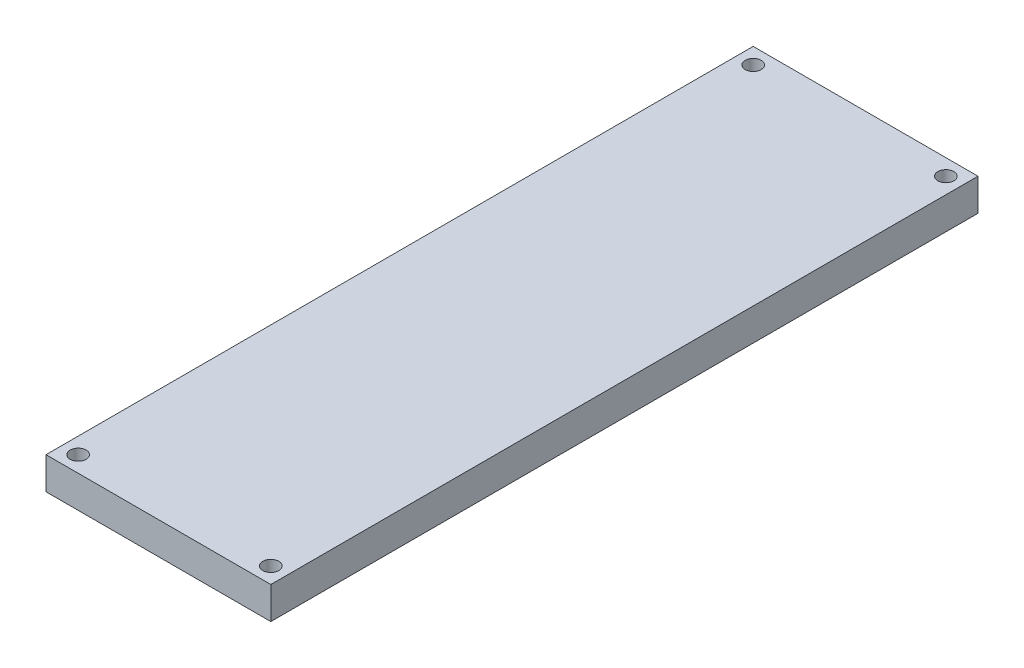
SolidWorks part; units mm, degrees
material "6061-T6 (SS)"
ref_plane "Front Plane" through (0, 0, 0) normal (0, 0, 1) x (1, 0, 0)
ref_plane "Top Plane" through (0, 0, 0) normal (0, 1, 0) x (1, 0, 0)
ref_plane "Right Plane" through (0, 0, 0) normal (1, 0, 0) x (0, 0, -1)
sketch "Sketch1" plane through (0, 0, 0) normal (0, 1, 0) x (1, 0, 0)
  line L1 (44.4136, -139.7) -> (-44.4136, -139.7)
  line L2 (44.4136, -139.7) -> (44.4136, 139.7)
  line L3 (44.4136, 139.7) -> (-44.4136, 139.7)
  line L4 (-44.4136, -139.7) -> (-44.4136, 139.7)
  line L5 (44.4136, -139.7) -> (-44.4136, 139.7) construction
  line L6 (44.4136, 139.7) -> (-44.4136, -139.7) construction
  line L8 (-44.4136, 139.7) -> (44.4136, -139.7) construction
  line L9 (44.4136, 139.7) -> (-44.4136, -139.7) construction
  point P0 (0, 0)
  point P5 (0, 0)
  dimension "D1" = 279.4
  dimension "D2" = 88.8273
extrude "Base Shape" add sketch "Sketch1" along normal blind 12.7
sketch "Sketch2" plane through (0, 12.7, 0) normal (0, 1, 0) x (1, 0, 0)
  line L0 (-38.0636, 139.7) -> (-38.0636, 133.35) construction
  line L1 (44.4136, 139.7) -> (-44.4136, 139.7) construction
  line L2 (-38.0636, 133.35) -> (-44.4136, 133.35) construction
  line L3 (-44.4136, 139.7) -> (-44.4136, -139.7) construction
  line L4 (0, 139.7) -> (0, -139.7) construction
  line L5 (-44.4136, -139.7) -> (44.4136, -139.7) construction
  line L6 (-44.4136, 0) -> (44.4136, 0) construction
  line L7 (44.4136, -139.7) -> (44.4136, 139.7) construction
  circle A0 centre (-38.0636, 133.35) radius 3.175
  circle A1 centre (38.0636, 133.35) radius 3.175
  circle A2 centre (38.0636, -133.35) radius 3.175
  circle A3 centre (-38.0636, -133.35) radius 3.175
  point P18 (0, 0)
  dimension "D3" = 6.35
  dimension "D1" = 6.35
  dimension "D2" = 6.35
extrude "0.25\" Diameter Clearance Holes for Assembly" cut sketch "Sketch2" against normal blind 12.7 contours A3 | A2 | A0 | A1
equation "\"Pipe Diameter\"= 1in"
equation "\"Pipe Radial Distance\"= 3.01in"
equation "\"Rocket Diameter\"= 12in"
equation "\"Airframe Thickness\"= 0.125in"
equation "\"Arduino Mega Length\"= 101.52mm"
equation "\"Arduino Mega Width\"= 53.3mm"
equation "\"Interior Height\"= 2in"
equation "\"Wall Thickness\"= 0.5in"
equation "\"Assembly Hole Diameter\"= 0.25in"
equation "\"4-40 Standoff Depth\"= 0.1875in"
equation "\"Wire Hole Diameter\"= 0.1in"
equation "\"D1\"= \"Wall Thickness\""
equation "\"Lid Length\"= ( 2 * \"Wall Thickness\" ) + ( \"Arduino Mega Length\" * 1.25 )"
equation "\"Lid Width\"= ( 2 * \"Wall Thickness\" ) + ( \"Arduino Mega Width\" * 1.25 )"
equation "\"D1@Base Shape\"=\"Wall Thickness\""
equation "\"D3@Sketch2\"=\"Assembly Hole Diameter\""
